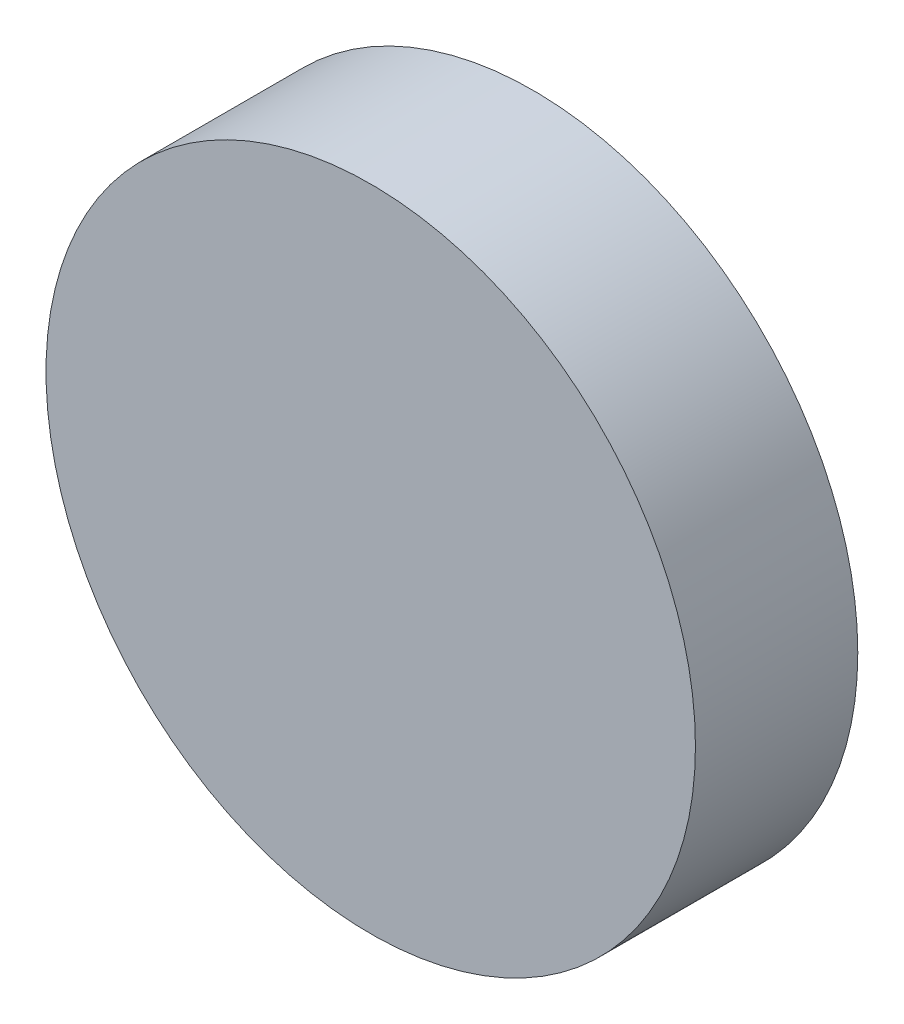
SolidWorks part; units mm, degrees
ref_plane "Front Plane" through (0, 0, 0) normal (0, 0, 1) x (1, 0, 0)
ref_plane "Top Plane" through (0, 0, 0) normal (0, 1, 0) x (1, 0, 0)
ref_plane "Right Plane" through (0, 0, 0) normal (1, 0, 0) x (0, 0, -1)
sketch "Sketch1" plane through (0, 0, 0) normal (0, 0, 1) x (1, 0, 0)
  circle A0 centre (0, 0) radius 40
extrude "Boss-Extrude1" add sketch "Sketch1" along normal blind 20
